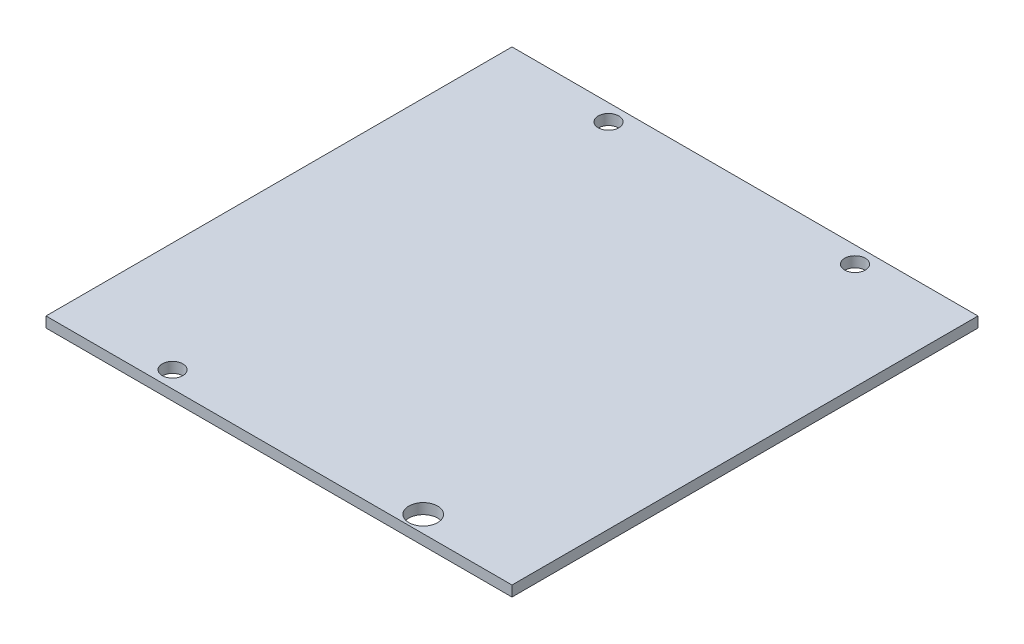
SolidWorks part; units mm, degrees
ref_plane "Front Plane" through (0, 0, 0) normal (0, 0, 1) x (1, 0, 0)
ref_plane "Top Plane" through (0, 0, 0) normal (0, 1, 0) x (1, 0, 0)
ref_plane "Right Plane" through (0, 0, 0) normal (1, 0, 0) x (0, 0, -1)
sketch "Sketch1" plane through (0, 0, 0) normal (0, 1, 0) x (1, 0, 0)
  line L1 (0, 0) -> (88.9, 0)
  line L2 (0, 0) -> (0, -88.9)
  line L3 (0, -88.9) -> (88.9, -88.9)
  line L4 (88.9, 0) -> (88.9, -88.9)
extrude "Boss-Extrude1" add sketch "Sketch1" along normal blind 2
sketch "Sketch2" plane through (0, 2, 0) normal (0, 1, 0) x (1, 0, 0)
  line L0 (19.6298, -3.175) -> (23.5548, -3.175) construction
  line L3 (19.6298, -6.35) -> (19.6298, 0) construction
  line L6 (23.5548, -6.35) -> (23.5548, 0) construction
  line L7 (21.5923, -6.35) -> (21.5923, 0) construction
  line L8 (23.5548, -6.35) -> (19.6298, -6.35) construction
  line L9 (13.9116, 0) -> (29.2731, 0) construction
  line L10 (66.6453, -3.175) -> (70.5753, -3.175) construction
  line L11 (66.6453, -6.35) -> (66.6453, 0) construction
  line L12 (70.5753, 0) -> (70.5753, -6.35) construction
  line L13 (68.3241, -6.3265) -> (68.3241, 0) construction
  line L14 (69.9116, -6.3265) -> (66.7366, -6.3265) construction
  line L15 (88.9, 0) -> (0, 0) construction
  line L16 (66.0088, -85.7015) -> (69.9387, -85.7015) construction
  line L17 (66.0088, -88.8765) -> (66.0088, -82.5265) construction
  line L18 (69.9387, -82.5265) -> (69.9387, -88.8765) construction
  line L19 (68.3241, -82.5265) -> (69.1871, -88.853) construction
  line L22 (69.9116, -82.5265) -> (66.7366, -82.5265) construction
  line L23 (71.1471, -88.853) -> (67.227, -88.853) construction
  line L24 (18.9933, -85.7015) -> (22.9183, -85.7015) construction
  line L25 (18.9933, -88.8765) -> (18.9933, -82.5265) construction
  line L26 (22.9183, -88.8765) -> (22.9183, -82.5265) construction
  line L27 (20.9558, -88.9) -> (20.9558, -82.5265) construction
  line L28 (0, -88.9) -> (88.9, -88.9) construction
  line L29 (22.9183, -82.5265) -> (18.9933, -82.5265) construction
  circle A1 centre (21.5923, -3.175) radius 1.9625
  circle A2 centre (68.6103, -3.175) radius 1.965
  circle A3 centre (68.7556, -85.6898) radius 2.7468
  circle A4 centre (20.9558, -85.7133) radius 1.9625
extrude "Cut-Extrude1" cut sketch "Sketch2" against normal through all
